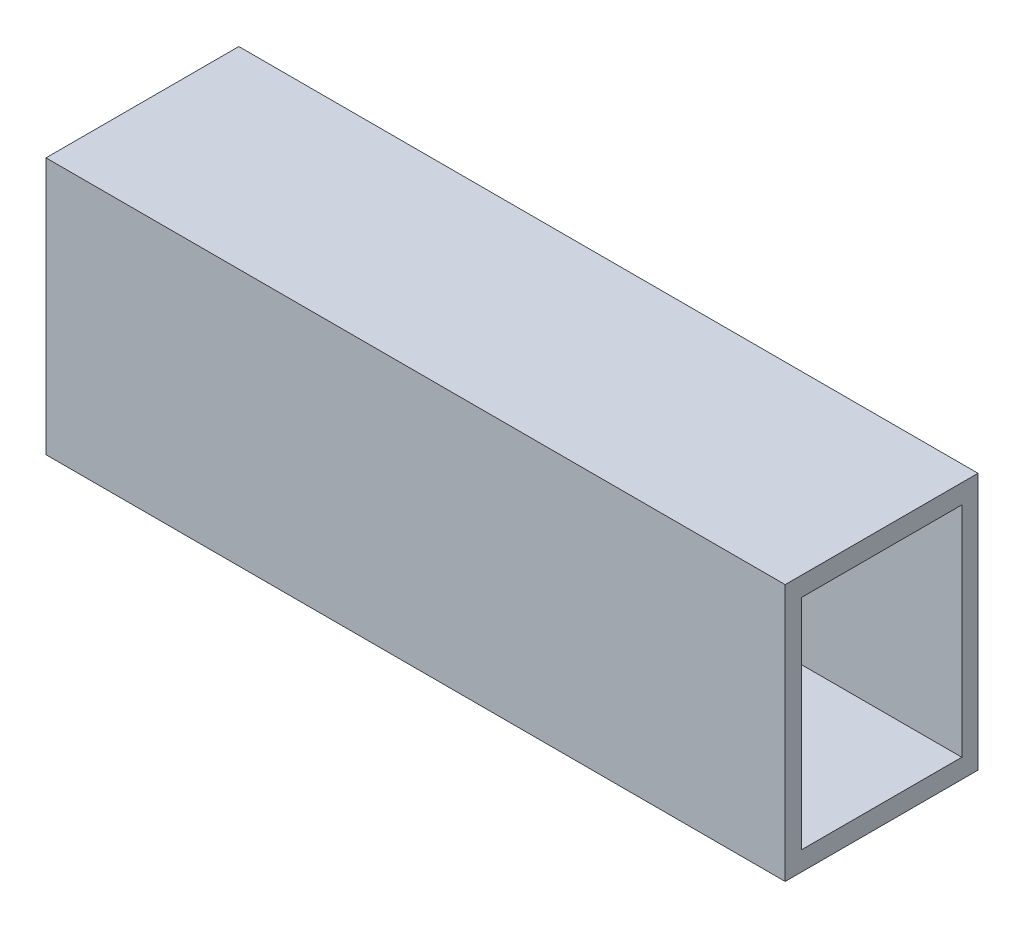
SolidWorks part; units mm, degrees
ref_plane "Front Plane" through (0, 0, 0) normal (0, 0, 1) x (1, 0, 0)
ref_plane "Top Plane" through (0, 0, 0) normal (0, 1, 0) x (1, 0, 0)
ref_plane "Right Plane" through (0, 0, 0) normal (1, 0, 0) x (0, 0, -1)
sketch "Croquis1" plane through (0, 0, 0) normal (1, 0, 0) x (0, 0, -1)
  line L0 (-15, -20) -> (-15, 20)
  line L1 (-15, -20) -> (15, -20)
  line L2 (-15, 20) -> (15, 20)
  line L3 (15, -20) -> (15, 20)
  line L4 (-15, -20) -> (15, 20) construction
  line L5 (-15, 20) -> (15, -20) construction
  line L6 (-12.4805, -17) -> (-12.4805, 17)
  line L7 (-12.4805, -17) -> (12.4805, -17)
  line L8 (-12.4805, 17) -> (12.4805, 17)
  line L9 (12.4805, -17) -> (12.4805, 17)
  line L10 (-12.4805, -17) -> (12.4805, 17) construction
  line L11 (-12.4805, 17) -> (12.4805, -17) construction
  point P0 (-15, 0)
  point P1 (0, 0)
  point P2 (0, 0)
  dimension "D1" = 40
  dimension "D2" = 30
  dimension "D3" = 3
  dimension "D4" = 2.5195
extrude "Saliente-Extruir1" add sketch "Croquis1" along normal blind 115
